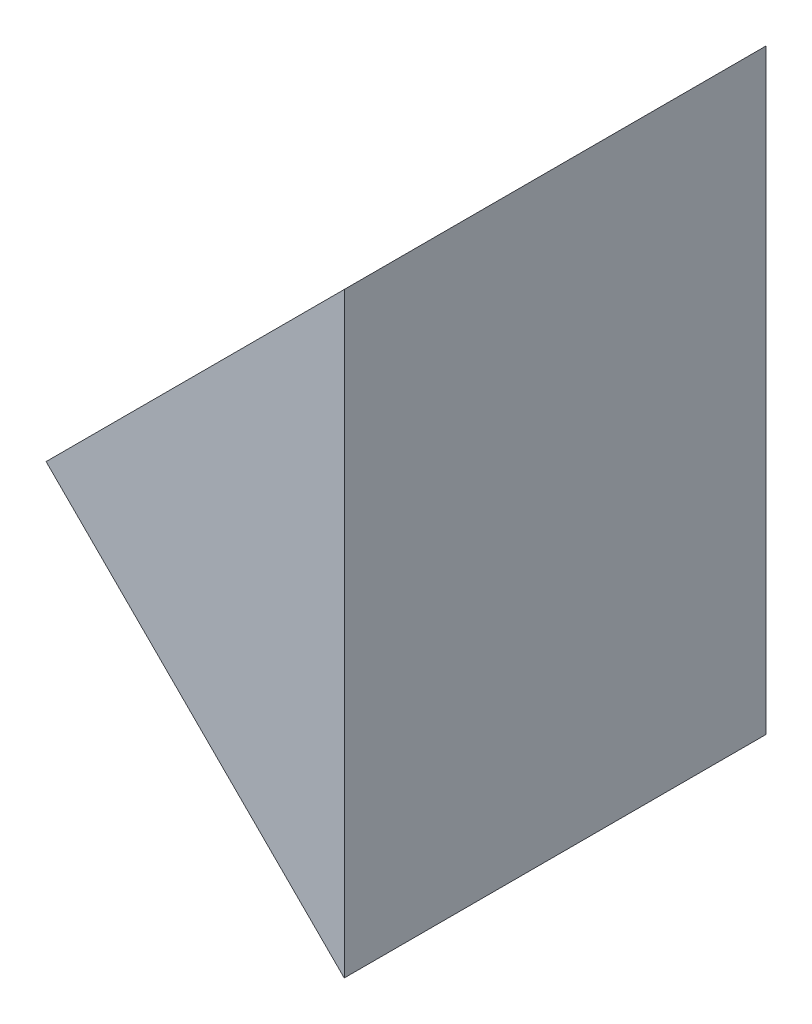
SolidWorks part; units mm, degrees
ref_plane "前视基准面" through (0, 0, 0) normal (0, 0, 1) x (1, 0, 0)
ref_plane "上视基准面" through (0, 0, 0) normal (0, 1, 0) x (1, 0, 0)
ref_plane "右视基准面" through (0, 0, 0) normal (1, 0, 0) x (0, 0, -1)
sketch "草图1" plane through (0, 0, 0) normal (0, 0, 1) x (1, 0, 0)
  line L0 (277.3833, 68.8785) -> (295.061, 86.5561)
  line L1 (277.3833, 68.8785) -> (295.061, 51.2008)
  line L2 (295.061, 51.2008) -> (295.061, 86.5561)
  dimension "D1" = 25
  dimension "D2" = 25
extrude "凸台-拉伸1" add sketch "草图1" along normal blind 25
